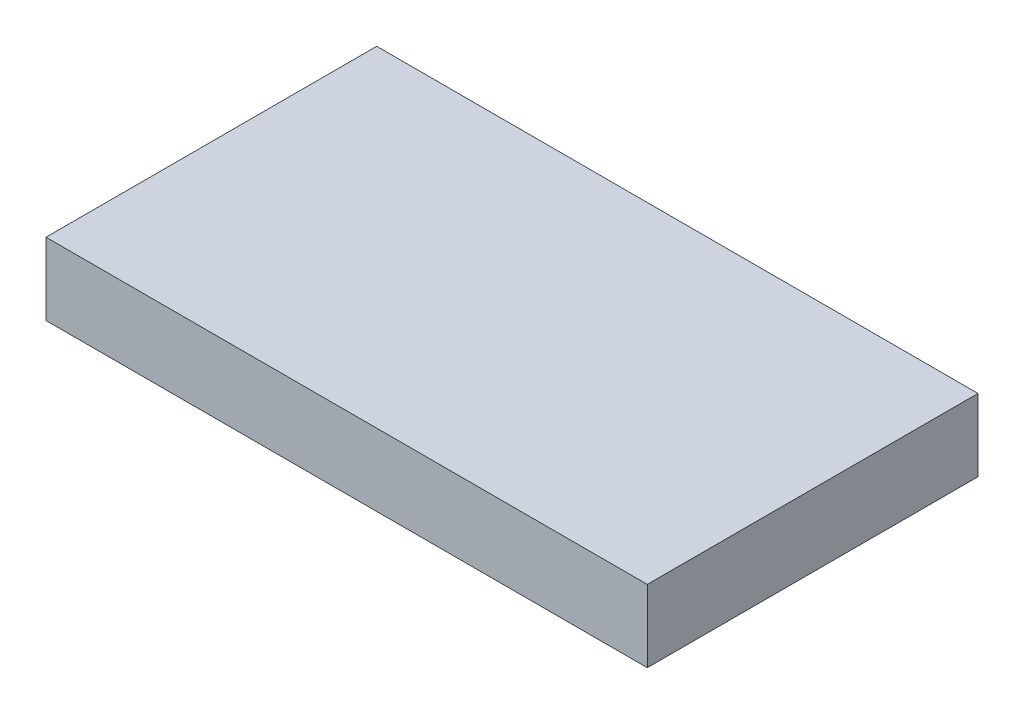
SolidWorks part; units mm, degrees
ref_plane "Plan de face" through (0, 0, 0) normal (0, 0, 1) x (1, 0, 0)
ref_plane "Plan de dessus" through (0, 0, 0) normal (0, 1, 0) x (1, 0, 0)
ref_plane "Plan de droite" through (0, 0, 0) normal (1, 0, 0) x (0, 0, -1)
sketch "Esquisse1" plane through (0, 0, 0) normal (0, 1, 0) x (1, 0, 0)
  line L1 (0, 0) -> (100, 0)
  line L2 (0, 0) -> (0, 55)
  line L3 (0, 55) -> (100, 55)
  line L4 (100, 0) -> (100, 55)
  dimension "D1" = 100
  dimension "D2" = 55
extrude "Boss.-Extru.1" add sketch "Esquisse1" along normal blind 12
